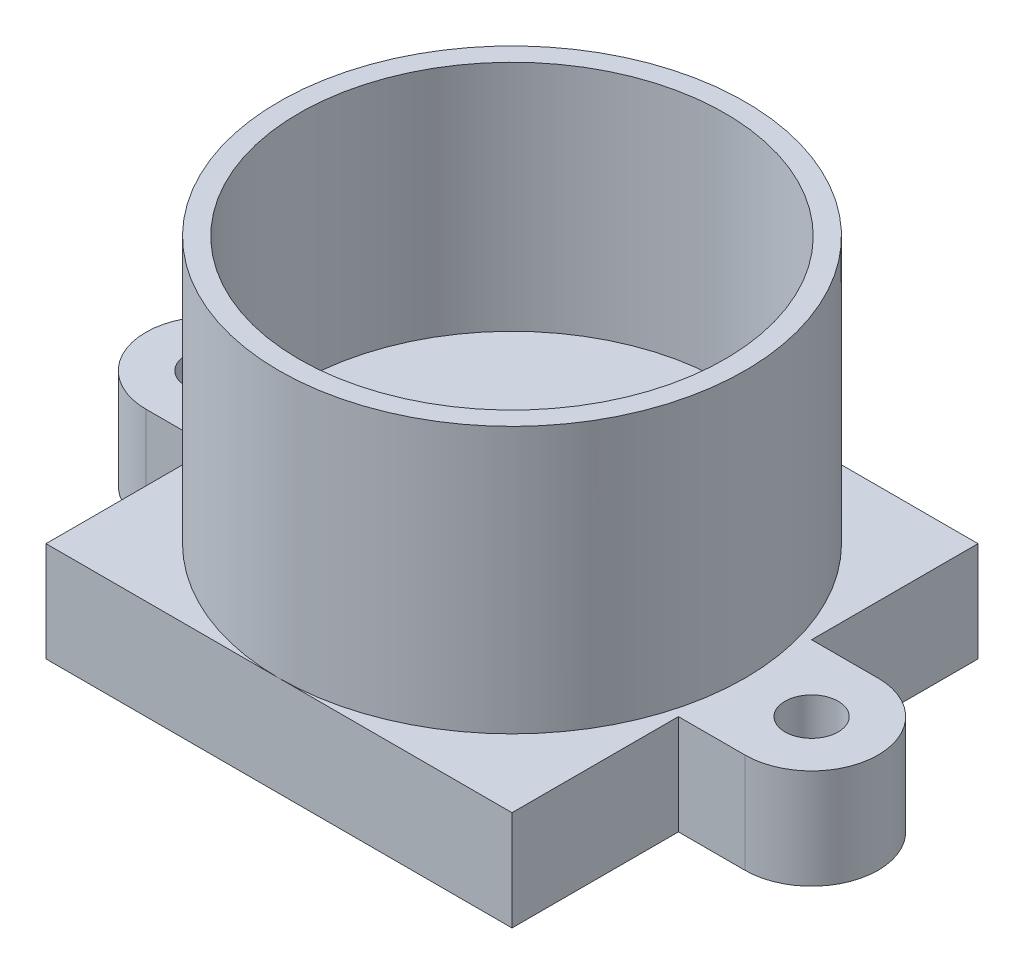
SolidWorks part; units mm, degrees
ref_plane "前视基准面" through (0, 0, 0) normal (0, 0, 1) x (1, 0, 0)
ref_plane "上视基准面" through (0, 0, 0) normal (0, 1, 0) x (1, 0, 0)
ref_plane "右视基准面" through (0, 0, 0) normal (1, 0, 0) x (0, 0, -1)
sketch "草图1" plane through (0, 0, 0) normal (0, 1, 0) x (1, 0, 0)
  line L1 (-7, 7) -> (7, 7)
  line L2 (-7, 7) -> (-7, -7)
  line L3 (-7, -7) -> (7, -7)
  line L4 (7, 7) -> (7, -7)
  line L5 (-7, 7) -> (7, -7) construction
  line L6 (-7, -7) -> (7, 7) construction
  point P0 (0, 0)
extrude "凸台-拉伸2" add sketch "草图1" along normal blind 3
sketch "草图2" plane through (0, 3, 0) normal (0, 1, 0) x (1, 0, 0)
  line L0 (-7, 7) -> (-7, -7) construction
  line L2 (-7, 0) -> (-7, 2)
  line L3 (-7, 2) -> (-9, 2)
  line L4 (-9, 0) -> (-9, 2)
  line L5 (7, -7) -> (7, 7) construction
  line L7 (-7, 0) -> (-7, -2)
  line L8 (-7, -2) -> (-9, -2)
  line L9 (-9, 0) -> (-9, -2)
  line L11 (7, 0) -> (7, 2)
  line L12 (7, 2) -> (9, 2)
  line L13 (9, 0) -> (9, 2)
  line L16 (7, 0) -> (7, -2)
  line L17 (7, -2) -> (9, -2)
  line L18 (9, 0) -> (9, -2)
extrude "凸台-拉伸4" add sketch "草图2" against normal blind 3
sketch "草图3" plane through (0, 3, 0) normal (0, 1, 0) x (1, 0, 0)
  line L2 (-9, 2) -> (-9, -2)
  line L4 (9, 2) -> (9, -2)
  arc A2 (-9, -2) -> (-9, 2) centre (-9, 0) cw
  arc A3 (9, 2) -> (9, -2) centre (9, 0) cw
extrude "凸台-拉伸5" add sketch "草图3" against normal blind 3
sketch "草图4" plane through (0, 3, 0) normal (0, 1, 0) x (1, 0, 0)
  circle A0 centre (-9, 0) radius 0.8
  circle A1 centre (9, 0) radius 0.8
extrude "切除-拉伸1" cut sketch "草图4" against normal blind 3
sketch "草图5" plane through (0, 3, 0) normal (0, 1, 0) x (1, 0, 0)
  circle A0 centre (0, 0) radius 7
extrude "凸台-拉伸6" add sketch "草图5" along normal blind 8
sketch "草图6" plane through (0, 11, 0) normal (0, 1, 0) x (1, 0, 0)
  circle A0 centre (0, 0) radius 6.4
extrude "切除-拉伸2" cut sketch "草图6" against normal blind 7
